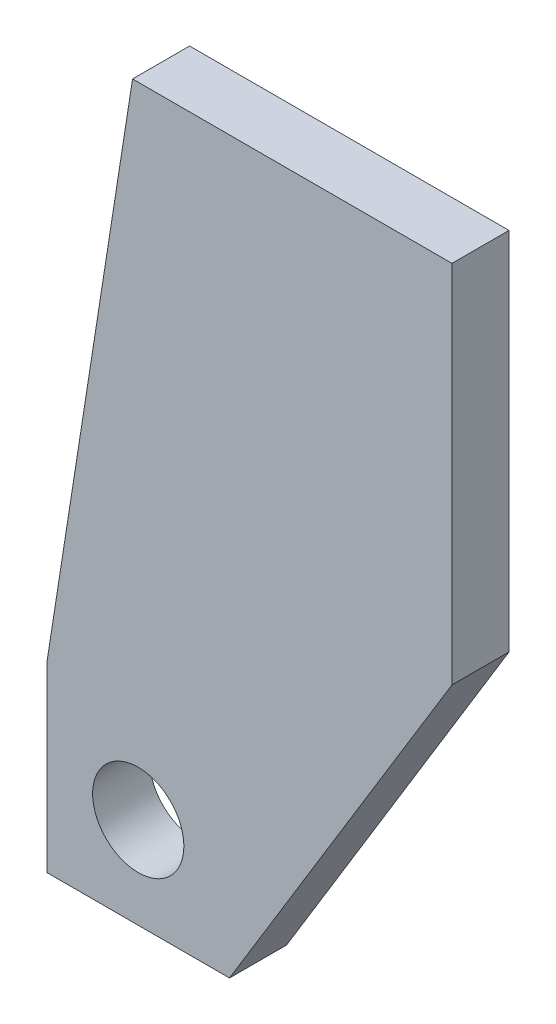
SolidWorks part; units mm, degrees
ref_plane "正面" through (0, 0, 0) normal (0, 0, 1) x (1, 0, 0)
ref_plane "平面" through (0, 0, 0) normal (0, 1, 0) x (1, 0, 0)
ref_plane "右側面" through (0, 0, 0) normal (1, 0, 0) x (0, 0, -1)
sketch "ｽｹｯﾁ1" plane through (0, 0, 0) normal (0, 0, 1) x (1, 0, 0)
  line L0 (0, 22) -> (16, 22)
  line L5 (16, 22) -> (35.5, 54)
  line L6 (35.5, 54) -> (35.5, 86)
  line L7 (35.5, 86) -> (7.5, 86)
  line L8 (7.5, 86) -> (0, 38)
  line L9 (0, 38) -> (0, 22)
  circle A1 centre (8, 30) radius 4 construction
  circle A2 centre (8, 30) radius 4
  point P15 (0, 60.7469)
  point P16 (0, 55.4023)
  point P17 (35.5, 38.0796)
  point P20 (35.5, 54)
  dimension "D1" = 8
  dimension "D2" = 8
  dimension "D4" = 8
  dimension "D5" = 16
extrude "ﾎﾞｽ - 押し出し1" add sketch "ｽｹｯﾁ1" along normal blind 5 from offset 20
